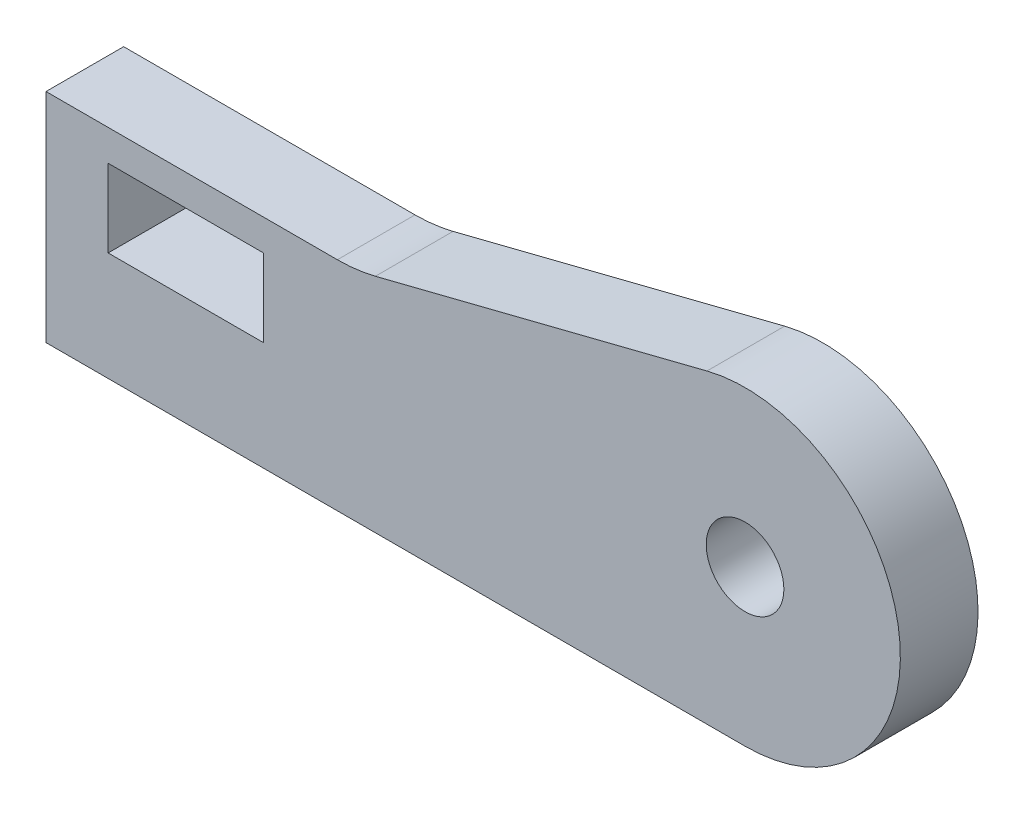
SolidWorks part; units mm, degrees
material "Acrylic (Medium-high impact)"
ref_plane "Front Plane" through (0, 0, 0) normal (0, 0, 1) x (1, 0, 0)
ref_plane "Top Plane" through (0, 0, 0) normal (0, 1, 0) x (1, 0, 0)
ref_plane "Right Plane" through (0, 0, 0) normal (1, 0, 0) x (0, 0, -1)
sketch "Sketch1" plane through (0, 0, 0) normal (0, 0, 1) x (1, 0, 0)
  line L0 (-24.3134, 0) -> (20.6866, 0)
  line L1 (-24.3134, 0) -> (-24.3134, 14)
  line L3 (30.6866, 10) -> (6.8806, 10) construction
  line L4 (20.6866, 20) -> (20.6866, 0) construction
  line L5 (-24.3134, 14) -> (-5.5567, 14)
  line L6 (-3.108, 14.3044) -> (18.2379, 19.6956)
  line L7 (-20.3134, 12) -> (-10.3134, 12)
  line L8 (-20.3134, 12) -> (-20.3134, 7)
  line L9 (-20.3134, 7) -> (-10.3134, 7)
  line L10 (-10.3134, 12) -> (-10.3134, 7)
  circle A0 centre (20.6866, 10) radius 2.5
  arc A1 (20.6866, 0) -> (18.2379, 19.6956) centre (20.6866, 10) ccw
  arc A2 (-5.5567, 14) -> (-3.108, 14.3044) centre (-5.5567, 24) ccw
  point P16 (-4.3134, 14)
  dimension "D6" = 5
  dimension "D8" = 10
  dimension "D1" = 10
  dimension "D2" = 14
  dimension "D3" = 5
  dimension "D4" = 10
  dimension "D5" = 20
  dimension "D7" = 20
  dimension "D9" = 2
  dimension "D10" = 4
  dimension "D11" = 55
extrude "Boss-Extrude1" add sketch "Sketch1" along normal blind 5
